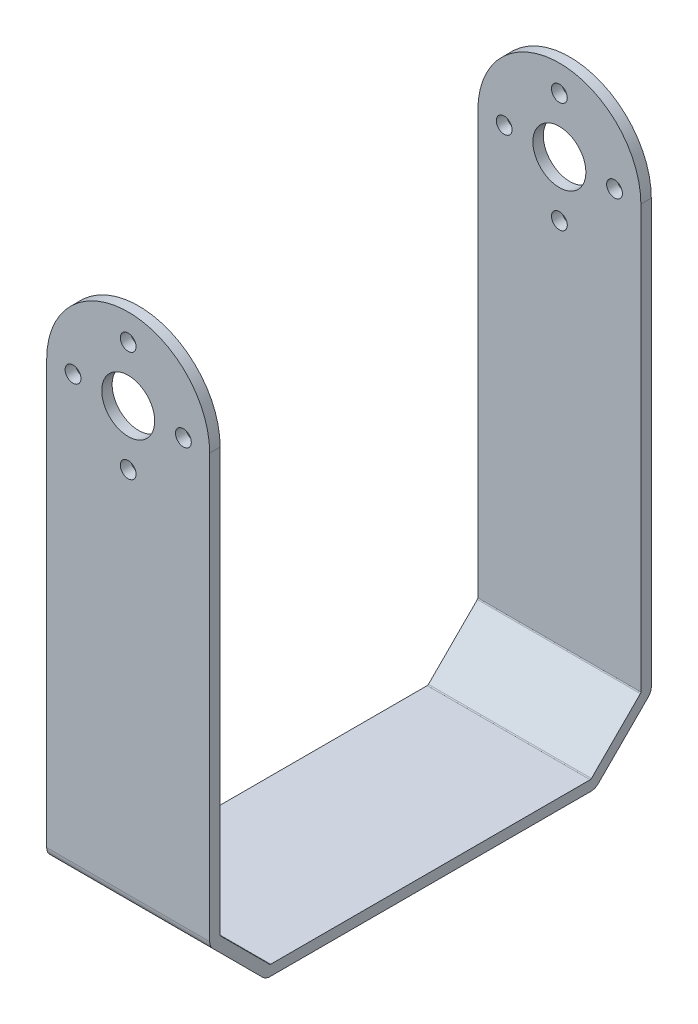
SolidWorks part; units mm, degrees
ref_plane "Front Plane" through (0, 0, 0) normal (0, 0, 1) x (1, 0, 0)
ref_plane "Top Plane" through (0, 0, 0) normal (0, 1, 0) x (1, 0, 0)
ref_plane "Right Plane" through (0, 0, 0) normal (1, 0, 0) x (0, 0, -1)
sketch "Sketch2" plane through (0, 0, 0) normal (1, 0, 0) x (0, 0, -1)
  line L1 (0, 0) -> (66.675, 0)
  line L2 (0, 0) -> (0, 85.3186)
  line L3 (0, 85.3186) -> (66.675, 85.3186)
  line L4 (66.675, 0) -> (66.675, 85.3186)
  dimension "D1" = 66.675
  dimension "D2" = 85.3186
extrude "Extrude1" add sketch "Sketch2" along normal blind 24.6126
sketch "Sketch3" plane through (24.6126, 0, 0) normal (1, 0, 0) x (0, 0, -1)
  line L0 (1.5748, 85.3186) -> (1.5748, 9.1186)
  line L1 (66.675, 85.3186) -> (0, 85.3186) construction
  line L2 (9.1186, 1.5748) -> (57.5564, 1.5748)
  line L3 (65.1002, 9.1186) -> (65.1002, 85.3186)
  line L4 (0, 85.3186) -> (0, 0) construction
  line L5 (0, 0) -> (66.675, 0) construction
  line L6 (66.675, 0) -> (66.675, 85.3186) construction
  line L7 (1.5748, 9.1186) -> (9.1186, 1.5748)
  line L8 (65.1002, 9.1186) -> (57.5564, 1.5748)
  line L9 (0, 8.4663) -> (8.4663, 0)
  line L10 (8.4663, 0) -> (58.2087, 0)
  line L11 (58.2087, 0) -> (66.675, 8.4663)
  line L12 (66.675, 8.4663) -> (66.675, 85.3186)
  line L13 (66.675, 85.3186) -> (65.1002, 85.3186)
  line L14 (1.5748, 85.3186) -> (0, 85.3186)
  line L15 (0, 85.3186) -> (0, 8.4663)
  dimension "D1" = 1.5748
  dimension "D2" = 1.5748
  dimension "D3" = 1.5748
  dimension "D4" = 9.1186
  dimension "D5" = 9.1186
  dimension "D6" = 9.1186
  dimension "D7" = 9.1186
  dimension "D8" = 1.5748
  dimension "D9" = 1.5748
extrude "Extrude2" cut sketch "Sketch3" against normal blind 24.6126 flip side to cut
sketch "Sketch4" plane through (0, 0, 0) normal (0, 0, 1) x (1, 0, 0)
  line L0 (24.6126, 85.3186) -> (0, 85.3186) construction
  line L1 (0, 73.0123) -> (0, 0)
  line L2 (0, 0) -> (24.6126, 0)
  line L3 (24.6126, 0) -> (24.6126, 73.0123)
  arc A0 (24.6126, 73.0123) -> (0, 73.0123) centre (12.3063, 73.0123) ccw
extrude "Extrude3" cut sketch "Sketch4" against normal through all flip side to cut
fillet "Fillet1" radius 1.5875 4 edges at (12.3063, 0, -58.2087) (12.3063, 8.4663, -66.675) (12.3063, 0, -8.4663) (12.3063, 8.4663, 0)
fillet "Fillet2" radius 0.254 4 edges at (12.3063, 9.1186, -65.1002) (12.3063, 1.5748, -57.5564) (12.3063, 1.5748, -9.1186) (12.3063, 9.1186, -1.5748)
sketch "Sketch5" plane through (0, 0, 0) normal (0, 0, 1) x (1, 0, 0)
  line L0 (24.6126, 0) -> (0, 0) construction
  circle A0 centre (12.3063, 73.025) radius 4.0005
  circle A1 centre (12.3063, 73.025) radius 8.3312 construction
  circle A2 centre (12.3063, 81.3562) radius 1.1938
  circle A3 centre (3.9751, 73.025) radius 1.1938
  circle A4 centre (12.3063, 64.6938) radius 1.1938
  circle A5 centre (20.6375, 73.025) radius 1.1938
  dimension "D1" = 8.001
  dimension "D2" = 73.025
extrude "Extrude4" cut sketch "Sketch5" against normal through all
